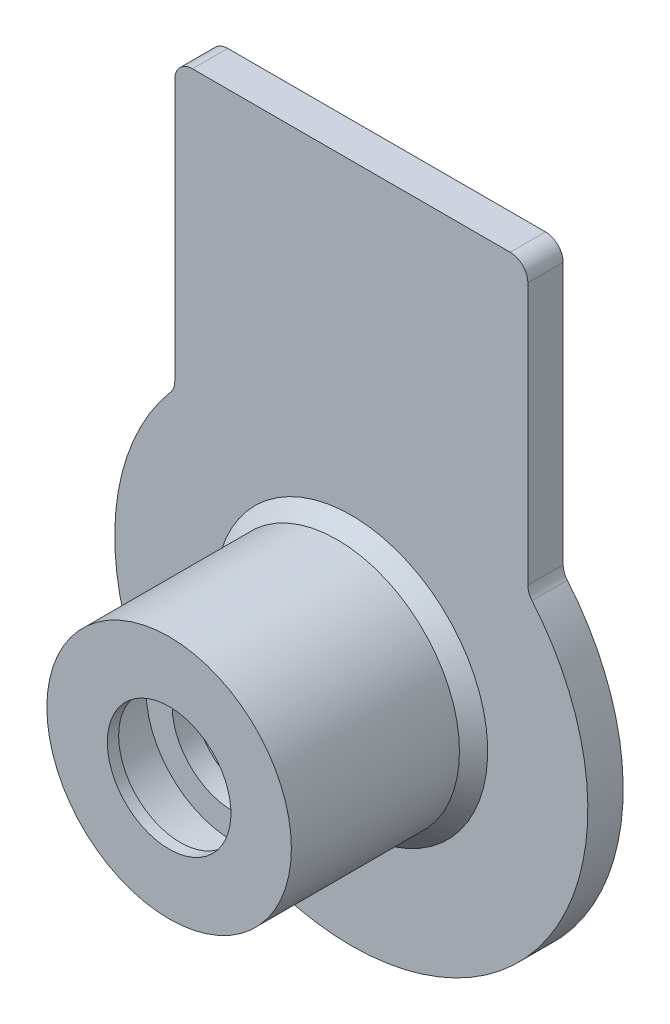
SolidWorks part; units mm, degrees
ref_plane "Front Plane" through (0, 0, 0) normal (0, 0, 1) x (1, 0, 0)
ref_plane "Top Plane" through (0, 0, 0) normal (0, 1, 0) x (1, 0, 0)
ref_plane "Right Plane" through (0, 0, 0) normal (1, 0, 0) x (0, 0, -1)
sketch "Sketch2" plane through (0, 0, 0) normal (0, 1, 0) x (1, 0, 0)
  line L0 (-3.5, -12.32) -> (-3.5, -11.68)
  line L1 (-3.5, -11.68) -> (-4.925, -11.2)
  line L2 (-4.925, -11.2) -> (-4.925, -8.7)
  line L3 (-4.925, -8.7) -> (-3.45, -8.7)
  line L4 (-3.45, -8.7) -> (-3.45, -7.5)
  line L5 (-3.45, -7.5) -> (-5, -7.5)
  line L6 (-3.5, -12.32) -> (-6.925, -12.32)
  line L7 (-6.925, -12.32) -> (-6.925, -2)
  line L8 (-5, -7.5) -> (-5, 0)
  line L12 (-13.4, 0) -> (-13.4, -2)
  line L13 (-13.4, -2) -> (-6.925, -2)
  line L14 (0, 0) -> (0, -12.32) construction
  line L15 (13.4, -2) -> (6.925, -2) construction
  line L16 (13.4, 0) -> (13.4, -2) construction
  line L20 (5, -7.5) -> (5, 0) construction
  line L21 (6.925, -12.32) -> (6.925, -2) construction
  line L22 (3.5, -12.32) -> (6.925, -12.32) construction
  line L23 (3.45, -7.5) -> (5, -7.5) construction
  line L24 (3.45, -8.7) -> (3.45, -7.5) construction
  line L25 (4.925, -8.7) -> (3.45, -8.7) construction
  line L26 (4.925, -11.2) -> (4.925, -8.7) construction
  line L27 (3.5, -11.68) -> (4.925, -11.2) construction
  line L28 (3.5, -12.32) -> (3.5, -11.68) construction
  line L31 (-5, 0) -> (-13.4, 0)
  line L34 (5, 0) -> (13.4, 0) construction
other "AlignGroup1"
other "AlignGroup2" parameters "D1"=6.1239, "D2"=15.6, "D3"=6.4543, "D4"=0.8, "D5"=10.0543, "D6"=6, "D7"=8.1501, "D8"=3.5773, "D9"=31.118, "D10"=2.5, "D11"=0.8, "D12"=5.3492, "D13"=1.7, "D14"=0.819, "D15"=0.3, "D16"=2.2
revolve "Revolve1" add sketch "Sketch2" angle 360 about L14
sketch "Sketch3" plane through (0, 0, 2) normal (0, 0, 1) x (1, 0, 0)
  line L0 (10, 8.9196) -> (10, 25.1216)
  line L1 (10, 25.1216) -> (-10, 25.1216)
  line L2 (-10, 25.1216) -> (-10, 8.9196)
  line L3 (0, 0) -> (-8, 8.1216) construction
  line L4 (-8, 8.1216) -> (-10, 8.1216) construction
  circle A0 centre (0, 0) radius 13.4 construction
  arc A1 (-10, 8.9196) -> (10, 8.9196) centre (0, 0) cw
  circle A2 centre (0, 0) radius 11.4 construction
  dimension "D2" = 22.8
  dimension "D1" = 20
  dimension "D3" = 2
  dimension "D4" = 17
extrude "Boss-Extrude1" add sketch "Sketch3" against normal up to surface (2 mm away) up to face at (-13.4, 0, 0)
fillet "Fillet2" radius 1 4 edges at (10, 8.9196, 1) (10, 25.1216, 1) (-10, 8.9196, 1) (-10, 25.1216, 1)
chamfer "Chamfer1" distance 0.8 angle 45 1 edges at (-6.925, 0, 2)
